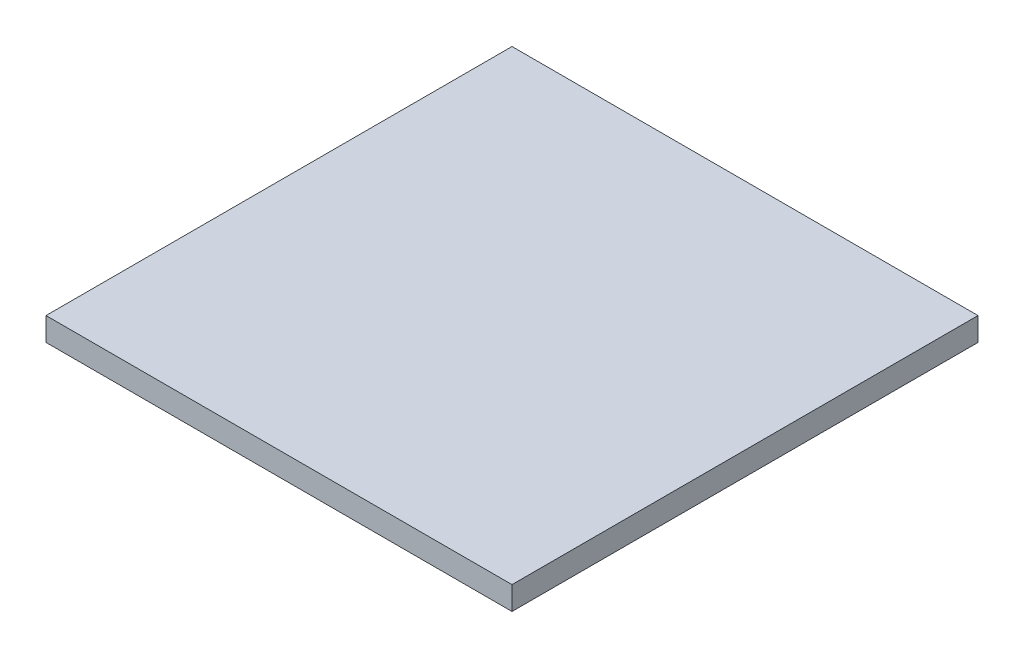
SolidWorks part; units mm, degrees
ref_plane "Спереди" through (0, 0, 0) normal (0, 0, 1) x (1, 0, 0)
ref_plane "Сверху" through (0, 0, 0) normal (0, 1, 0) x (1, 0, 0)
ref_plane "Справа" through (0, 0, 0) normal (1, 0, 0) x (0, 0, -1)
sketch "Эскиз1" plane through (0, 0, 0) normal (0, 1, 0) x (1, 0, 0)
  line L1 (-100, 100) -> (100, 100)
  line L2 (-100, 100) -> (-100, -100)
  line L3 (-100, -100) -> (100, -100)
  line L4 (100, 100) -> (100, -100)
  line L5 (-100, 100) -> (100, -100) construction
  line L6 (-100, -100) -> (100, 100) construction
  point P0 (0, 0)
  dimension "D1" = 200
extrude "Бобышка-Вытянуть1" add sketch "Эскиз1" along normal blind 10
